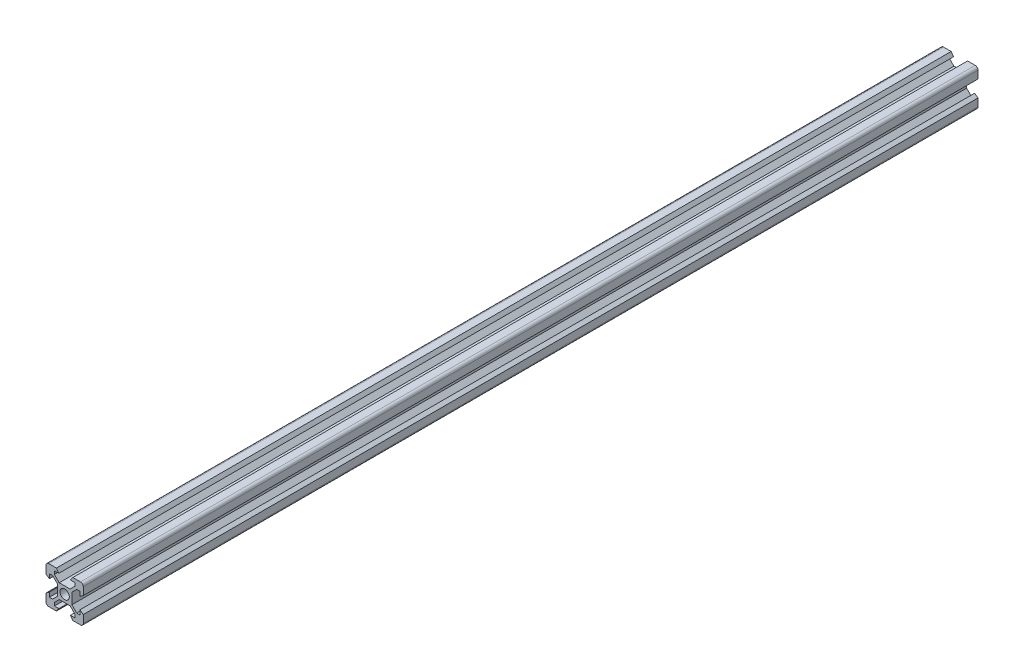
SolidWorks part; units mm, degrees
ref_plane "前视基准面" through (0, 0, 0) normal (0, 0, 1) x (1, 0, 0)
ref_plane "上视基准面" through (0, 0, 0) normal (0, 1, 0) x (1, 0, 0)
ref_plane "右视基准面" through (0, 0, 0) normal (1, 0, 0) x (0, 0, -1)
sketch "草图1" plane through (0, 0, 0) normal (0, 0, 1) x (1, 0, 0)
  line L0 (16.8101, 19.3214) -> (19.4, 21.9114) construction
  line L1 (14.8, 34.8214) -> (18.9, 34.8214)
  line L2 (13.3, 33.3214) -> (13.3, 29.2214)
  line L3 (14.8, 14.8214) -> (18.9, 14.8214)
  line L4 (33.3, 33.3214) -> (33.3, 29.2214)
  line L7 (27.2, 27.7315) -> (29.7899, 30.3214) construction
  line L8 (33.3, 29.2214) -> (31.5, 27.9214)
  line L9 (28.8, 31.3114) -> (26.2101, 28.7214)
  line L10 (31.5, 30.3214) -> (31.5, 27.9214)
  line L11 (29.7899, 30.3214) -> (31.5, 30.3214)
  line L12 (26.2101, 28.7214) -> (28.8, 31.3114) construction
  line L13 (27.2, 27.7315) -> (29.7899, 30.3214)
  line L15 (20.3899, 28.7214) -> (26.2101, 28.7214) construction
  line L18 (18.9, 34.8214) -> (20.2, 33.0214)
  line L19 (27.7, 34.8214) -> (26.4, 33.0214)
  line L20 (26.4, 33.0214) -> (28.8, 33.0214)
  line L21 (28.8, 33.0214) -> (28.8, 31.3114)
  line L22 (26.2101, 28.7214) -> (20.3899, 28.7214)
  line L25 (20.3899, 28.7214) -> (17.8, 31.3114)
  line L26 (17.8, 31.3114) -> (17.8, 33.0214)
  line L27 (17.8, 33.0214) -> (20.2, 33.0214)
  line L28 (27.2, 21.9114) -> (27.2, 27.7315)
  line L29 (29.7899, 19.3214) -> (27.2, 21.9114)
  line L30 (31.5, 19.3214) -> (29.7899, 19.3214)
  line L31 (31.5, 21.7214) -> (31.5, 19.3214)
  line L32 (33.3, 20.4214) -> (31.5, 21.7214)
  line L33 (27.7, 14.8214) -> (26.4, 16.6214)
  line L34 (28.8, 16.6214) -> (26.4, 16.6214)
  line L35 (28.8, 18.3315) -> (28.8, 16.6214)
  line L36 (26.2101, 20.9214) -> (28.8, 18.3315)
  line L37 (20.3899, 20.9214) -> (26.2101, 20.9214)
  line L38 (17.8, 18.3315) -> (20.3899, 20.9214)
  line L39 (17.8, 16.6214) -> (17.8, 18.3315)
  line L40 (20.2, 16.6214) -> (17.8, 16.6214)
  line L41 (18.9, 14.8214) -> (20.2, 16.6214)
  line L42 (13.3, 20.4214) -> (15.1, 21.7214)
  line L43 (15.1, 19.3214) -> (15.1, 21.7214)
  line L44 (16.8101, 19.3214) -> (15.1, 19.3214)
  line L45 (19.4, 21.9114) -> (16.8101, 19.3214)
  line L46 (19.4, 27.7315) -> (19.4, 21.9114)
  line L47 (16.8101, 30.3214) -> (19.4, 27.7315)
  line L48 (15.1, 30.3214) -> (16.8101, 30.3214)
  line L49 (15.1, 27.9214) -> (15.1, 30.3214)
  line L50 (13.3, 29.2214) -> (15.1, 27.9214)
  line L51 (27.7, 34.8214) -> (31.8, 34.8214)
  line L52 (33.3, 20.4214) -> (33.3, 16.3214)
  line L53 (13.3, 20.4214) -> (13.3, 16.3214)
  line L54 (27.7, 14.8214) -> (31.8, 14.8214)
  circle A0 centre (23.3, 24.8214) radius 2.5
  arc A1 (14.8, 34.8214) -> (13.3, 33.3214) centre (14.8, 33.3214) ccw
  arc A2 (33.3, 33.3214) -> (31.8, 34.8214) centre (31.8, 33.3214) ccw
  arc A3 (31.8, 14.8214) -> (33.3, 16.3214) centre (31.8, 16.3214) ccw
  arc A4 (14.8, 14.8214) -> (13.3, 16.3214) centre (14.8, 16.3214) cw
  point P11 (33.3, 34.8214)
  point P18 (33.3, 14.8214)
  dimension "D3" = 5
  dimension "D1" = 1.5
  dimension "D4" = 1.5
  dimension "D5" = 1.5
  dimension "D7" = 1.5
  dimension "D2" = 20
  dimension "D6" = 4
extrude "凸台-拉伸1" add sketch "草图1" along normal blind 480
